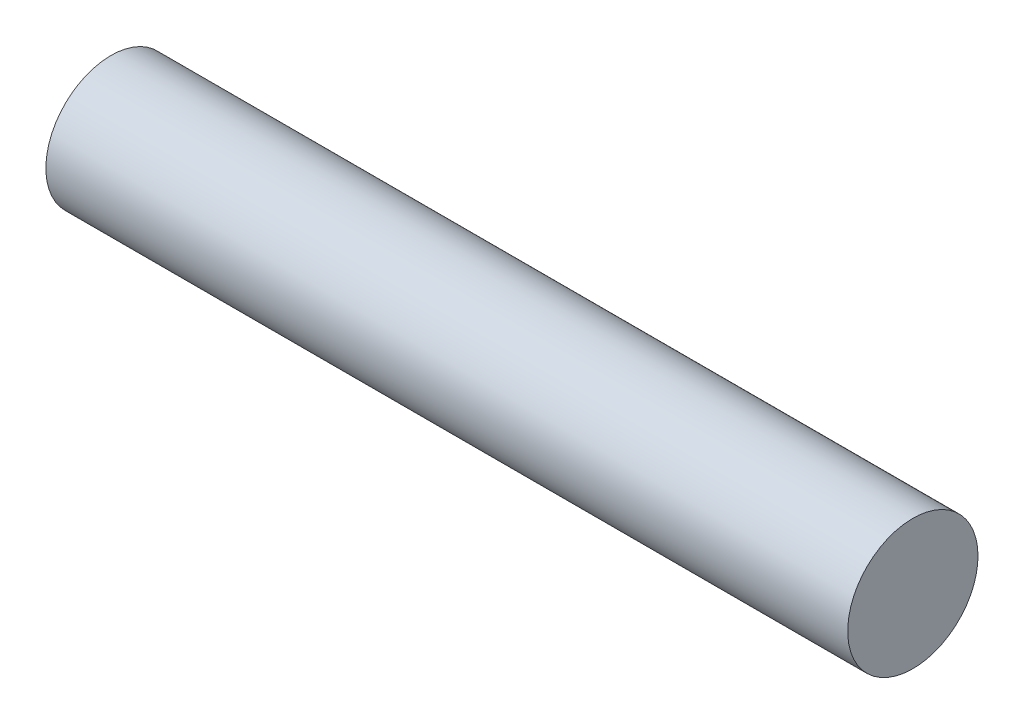
SolidWorks part; units mm, degrees
ref_plane "Front Plane" through (0, 0, 0) normal (0, 0, 1) x (1, 0, 0)
ref_plane "Top Plane" through (0, 0, 0) normal (0, 1, 0) x (1, 0, 0)
ref_plane "Right Plane" through (0, 0, 0) normal (1, 0, 0) x (0, 0, -1)
sketch "Sketch1" plane through (0, 0, 0) normal (1, 0, 0) x (0, 0, -1)
  circle A0 centre (0, 0) radius 3.25
  point P2 (-2.7691, -1.9775)
  dimension "D1" = 6.5
extrude "Boss-Extrude1" add sketch "Sketch1" along normal mid plane 40
